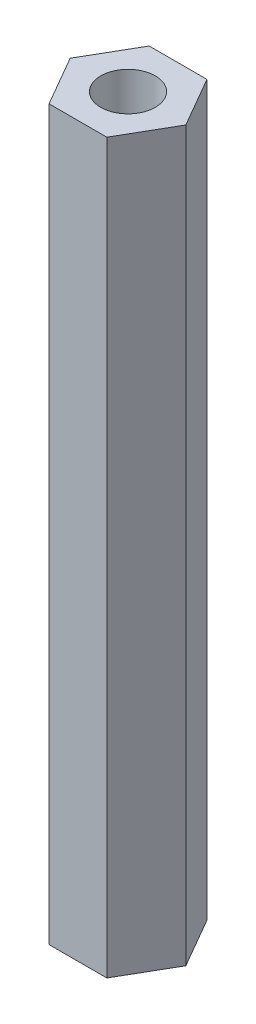
SolidWorks part; units mm, degrees
ref_plane "Front Plane" through (0, 0, 0) normal (0, 0, 1) x (1, 0, 0)
ref_plane "Top Plane" through (0, 0, 0) normal (0, 1, 0) x (1, 0, 0)
ref_plane "Right Plane" through (0, 0, 0) normal (1, 0, 0) x (0, 0, -1)
sketch "Sketch1" plane through (0, 0, 0) normal (0, 1, 0) x (1, 0, 0)
  line L1 (3.1754, 0) -> (1.5877, 2.75)
  line L2 (1.5877, 2.75) -> (-1.5877, 2.75)
  line L3 (-1.5877, 2.75) -> (-3.1754, 0)
  line L4 (-3.1754, 0) -> (-1.5877, -2.75)
  line L5 (-1.5877, -2.75) -> (1.5877, -2.75)
  line L6 (1.5877, -2.75) -> (3.1754, 0)
  circle A0 centre (0, 0) radius 2.75 construction
  dimension "D1" = 5.5
extrude "Boss-Extrude1" add sketch "Sketch1" along normal blind 40
sketch "Sketch2" plane through (0, 40, 0) normal (0, 1, 0) x (1, 0, 0)
  circle A0 centre (0, 0) radius 1.5
  dimension "D1" = 3
extrude "Cut-Extrude1" cut sketch "Sketch2" against normal blind 10
ref_plane "Plane1" through (0, 20, 0) normal (0, -1, 0) x (-1, 0, 0)
mirror "Mirror1" about plane through (0, 20, 0) normal (0, -1, 0) of "Cut-Extrude1"
